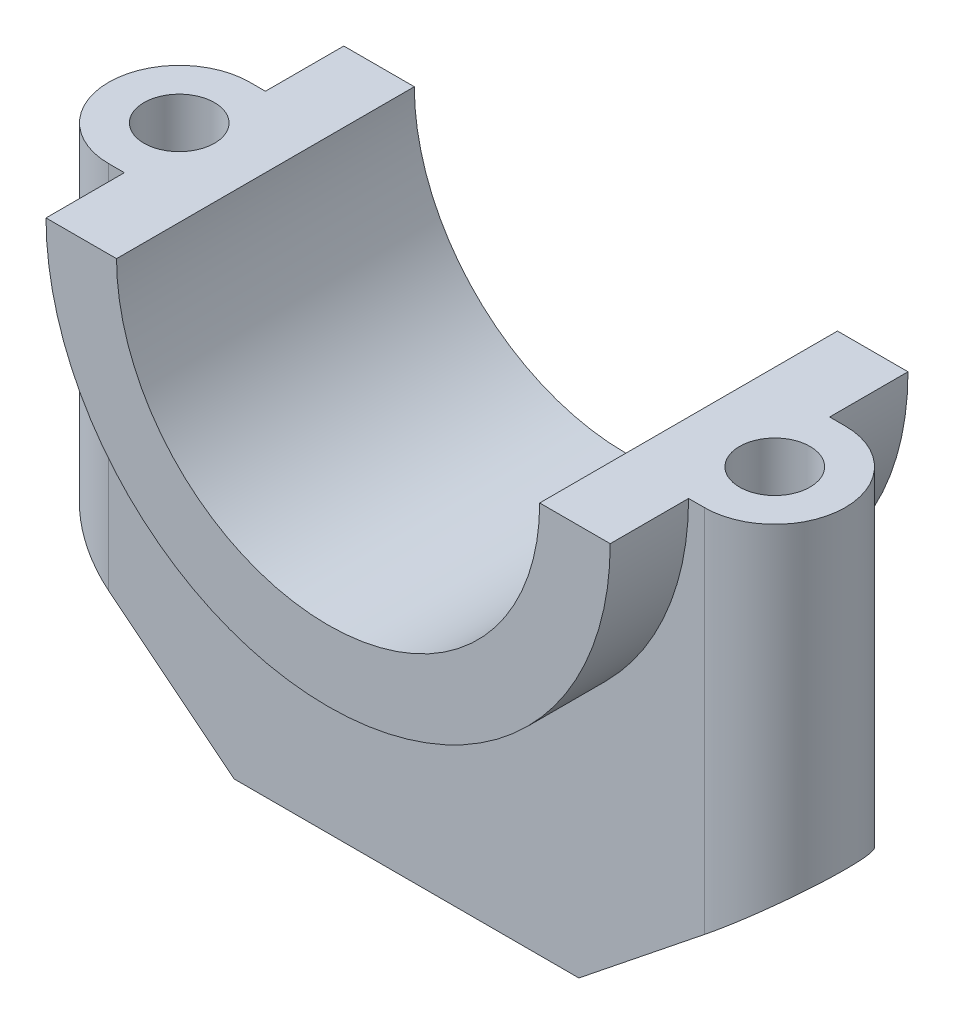
SolidWorks part; units mm, degrees
material "Cast Alloy Steel"
ref_plane "Front Plane" through (0, 0, 0) normal (0, 0, 1) x (1, 0, 0)
ref_plane "Top Plane" through (0, 0, 0) normal (0, 1, 0) x (1, 0, 0)
ref_plane "Right Plane" through (0, 0, 0) normal (1, 0, 0) x (0, 0, -1)
sketch "Sketch1" plane through (0, 0, 0) normal (0, 0, 1) x (1, 0, 0)
  line L1 (0, -465.5302) -> (0, 22810.9803) construction
  line L8 (-1000, 0) -> (-47, 0) construction
  line L9 (27, 0) -> (36, 0)
  line L10 (27, 0) -> (36, 0) construction
  line L12 (-36, 0) -> (-27, 0)
  line L13 (-27, 0) -> (27, 0)
  arc A3 (-36, 0) -> (36, 0) centre (0, 0) ccw
  dimension "D4" = 36
  dimension "D1" = 47
extrude "Boss-Extrude2" add sketch "Sketch1" along normal blind 38 contours A3 L9 L13 L12
ref_plane "Plane1" through (0, 0, 19) normal (0, 0, 1) x (1, 0, 0)
ref_plane "Plane2" through (0, 0, 19) normal (0, 0, 1) x (1, 0, 0)
sketch "Sketch3" plane through (0, 0, 38) normal (0, 0, 1) x (1, 0, 0)
  line L0 (-36, 0) -> (36, 0) construction
  line L1 (-27, 0) -> (27, 0)
  arc A0 (-27, 0) -> (27, 0) centre (0, 0) ccw
  dimension "D1" = 27
sketch "Sketch4" plane through (0, 0, 19) normal (0, 0, 1) x (1, 0, 0)
  line L0 (-36, 0) -> (-47, 0)
  line L1 (-47, 0) -> (-47, -40)
  line L2 (-47, -40) -> (-22, -60)
  line L3 (-22, -60) -> (22, -60)
  line L4 (0, -1000) -> (0, 49000) construction
  line L5 (47, -40) -> (22, -60)
  line L6 (47, 0) -> (47, -40)
  line L7 (36, 0) -> (47, 0)
  arc A0 (-36, 0) -> (36, 0) centre (0, 0) ccw construction
  arc A1 (-36, 0) -> (36, 0) centre (0, 0) ccw
  point P15 (0, -60)
  dimension "D1" = 47
  dimension "D2" = 60
  dimension "D3" = 25
  dimension "D4" = 20
extrude "Boss-Extrude3" add sketch "Sketch4" along normal mid plane 18
sketch "Sketch5" plane through (0, 0, 0) normal (0, 1, 0) x (1, 0, 0)
  line L0 (0, -1000) -> (0, 49000) construction
  line L1 (-1047, -19) -> (48953, -19) construction
  line L2 (-47, -28) -> (-47, -10) construction
  circle A0 centre (-38, -19) radius 9
  circle A1 centre (38, -19) radius 9
  point P8 (-47, -19)
  dimension "D1" = 18
  dimension "D2" = 76
extrude "Boss-Extrude4" add sketch "Sketch5" against normal blind 40
sketch "Sketch6" plane through (0, 0, 0) normal (0, 1, 0) x (1, 0, 0)
  line L0 (0, -1000) -> (0, 49000) construction
  line L1 (-1047, -19) -> (48953, -19) construction
  line L2 (-47, -28) -> (-47, -10) construction
  line L4 (-36, -10) -> (-47, -10) construction
  line L6 (-47, -19) -> (-47, -10)
  line L7 (-38, -10) -> (-47, -10)
  arc A2 (-47, -19) -> (-38, -10) centre (-38, -19) cw
  point P14 (-47, -19)
  dimension "D1" = 9
extrude "Cut-Extrude1" cut sketch "Sketch6" against normal through all contours L7 L6 A2
mirror "Mirror1" about plane through (0, 0, 19) normal (0, 0, 1) of "Cut-Extrude1"
mirror "Mirror2" about plane through (0, 0, 0) normal (1, 0, 0) of "Mirror1", "Cut-Extrude1"
extrude "Cut-Extrude3" cut sketch "Sketch3" against normal blind 40 contours A0 L1
sketch "Sketch7" plane through (0, 0, 0) normal (0, 1, 0) x (1, 0, 0)
  circle A0 centre (-38, -19) radius 4.5
  circle A1 centre (38, -19) radius 4.5
  arc A2 (-38, -10) -> (-38, -28) centre (-38, -19) ccw construction
  arc A3 (38, -28) -> (38, -10) centre (38, -19) ccw construction
  dimension "D1" = 9
extrude "Cut-Extrude4" cut sketch "Sketch7" against normal through all
